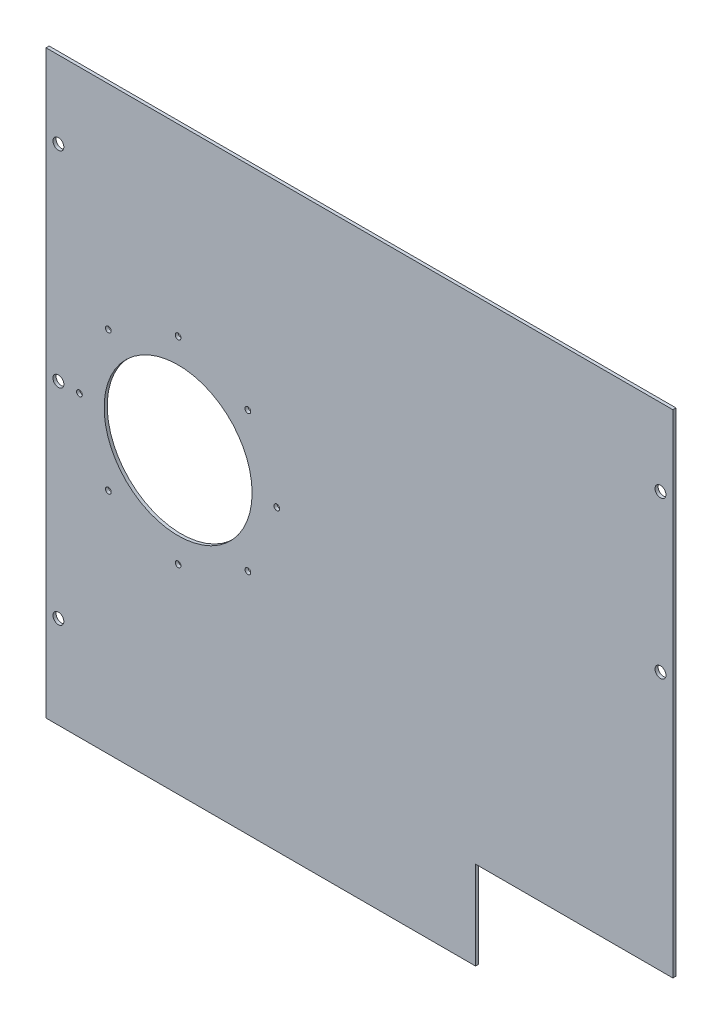
SolidWorks part; units mm, degrees
material "6061-T6 (SS)"
ref_plane "Front Plane" through (0, 0, 0) normal (0, 0, 1) x (1, 0, 0)
ref_plane "Top Plane" through (0, 0, 0) normal (0, 1, 0) x (1, 0, 0)
ref_plane "Right Plane" through (0, 0, 0) normal (1, 0, 0) x (0, 0, -1)
sketch "Sketch1" plane through (0, 0, 0) normal (0, 0, 1) x (1, 0, 0)
  line L0 (161.3627, -107.9357) -> (59.7625, -107.9357)
  line L1 (-161.3627, 145.4859) -> (161.3627, 145.4859)
  line L2 (-161.3627, 145.4859) -> (-161.3627, -153.4107)
  line L3 (-161.3627, -153.4107) -> (59.7625, -153.4107)
  line L4 (161.3627, 145.4859) -> (161.3627, -107.9357)
  line L5 (59.7625, -107.9357) -> (59.7625, -153.4107)
  line L6 (0, 0) -> (0, 57.0615) construction
  line L7 (59.7625, -153.4107) -> (161.3627, -153.4107) construction
  line L8 (161.3627, -107.9357) -> (161.3627, -153.4107) construction
  line L9 (0, 0) -> (-41.9055, 0) construction
  point P11 (0, 145.4859)
  dimension "D1" = 298.8966
  dimension "D2" = 322.7254
  dimension "D3" = 45.475
  dimension "D4" = 101.6002
  dimension "D5" = 153.4107
extrude "Boss-Extrude1" add sketch "Sketch1" along normal blind 1.6002
sketch "Sketch2" plane through (0, 0, 1.6002) normal (0, 0, 1) x (1, 0, 0)
  line L0 (0, 0) -> (39.3414, 0) construction
  line L1 (-161.3627, 145.4859) -> (-161.3627, -153.4107) construction
  circle A0 centre (-93.3627, 0) radius 38.1
  dimension "D1" = 76.2
  dimension "D2" = 68
extrude "Cut-Extrude1" cut sketch "Sketch2" against normal through all
sketch "Sketch10" plane through (0, 0, 1.6002) normal (0, 0, 1) x (1, 0, 0)
  line L0 (-93.3627, 0) -> (-93.3627, 50.8) construction
  dimension "D1" = 50.8
hole_wizard "#4 Clearance Hole1" positions "Sketch12" profile "Sketch11" hole size "#4" standard "ANSI Inch"
sketch "Sketch12" plane through (0, 0, 1.6002) normal (0, 0, 1) x (1, 0, 0)
  point P0 (-93.3627, 50.8)
sketch "Sketch11" plane through (-93.3627, 50.8, 1.6002) normal (1, 0, 0) x (0, -1, 0)
  line L0 (0, 0) -> (0, 173.8552)
  line L1 (0, 173.8552) -> (1.4732, 172.97)
  line L2 (1.4732, 172.97) -> (1.4732, 0)
  line L5 (1.4732, 0) -> (0, 0)
  line L10 (0, 173.8552) -> (-1.4732, 172.97) construction
  line L11 (0, -6.35) -> (0, 107.95) construction
  dimension "Hole Dia." = 2.9464
  dimension "Hole Depth" = 172.97
  dimension "Drill Angle" = 118
pattern_circular "CirPattern1" count 8 over 360 about axis through (-93.3627, 0, 0) along (0, 0, 1) of "#4 Clearance Hole1"
hole_wizard "#10 Clearance Hole1" positions "Sketch14" profile "Sketch13" hole size "#10" standard "ANSI Inch"
sketch "Sketch14" plane through (0, 0, 1.6002) normal (0, 0, 1) x (1, 0, 0)
  line L0 (0, 0) -> (78.2306, 0) construction
  line L1 (0, 0) -> (0, 74.3312) construction
  line L2 (-155, 105.7857) -> (-155, 68.2934) construction
  line L3 (155, 105.7857) -> (155, 57.6648) construction
  point P0 (-155, 105.7857)
  point P10 (-155, 0)
  point P13 (-155, -105.7857)
  point P14 (155, 105.7857)
  point P15 (155, 25.2785)
  dimension "D1" = 155
  dimension "D2" = 105.7857
  dimension "D3" = 25.2785
sketch "Sketch13" plane through (-155, 105.7857, 1.6002) normal (1, 0, 0) x (0, -1, 0)
  line L0 (0, 0) -> (0, 11.2164)
  line L1 (0, 11.2164) -> (2.8067, 9.53)
  line L2 (2.8067, 9.53) -> (2.8067, 0)
  line L5 (2.8067, 0) -> (0, 0)
  line L10 (0, 11.2164) -> (-2.8067, 9.53) construction
  line L11 (0, -6.35) -> (0, 107.95) construction
  dimension "Hole Dia." = 5.6134
  dimension "Hole Depth" = 9.53
  dimension "Drill Angle" = 118
